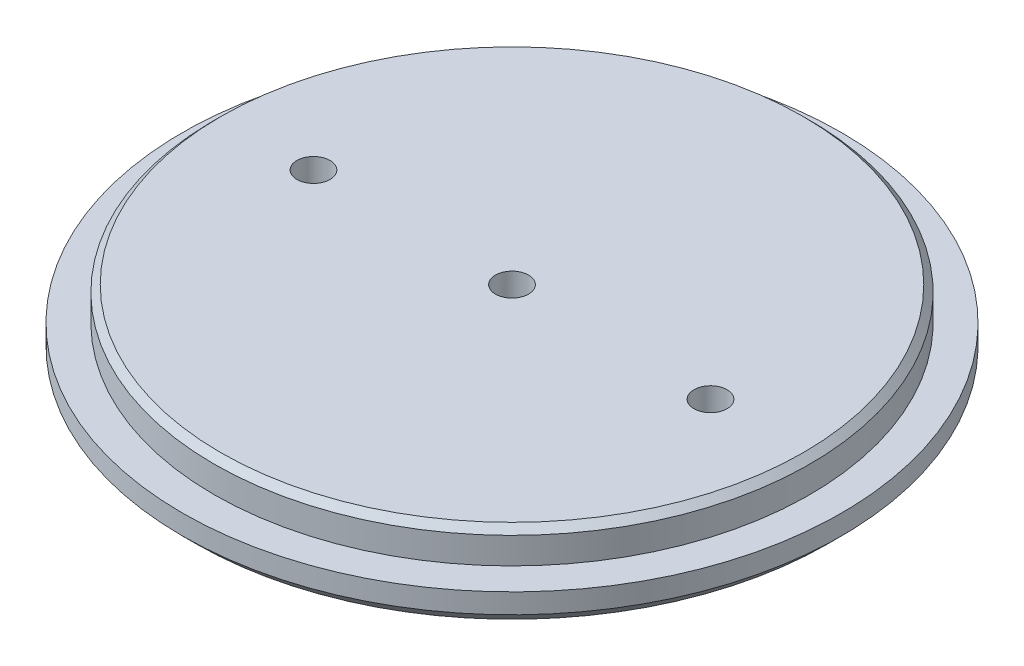
SolidWorks part; units mm, degrees
ref_plane "Front Plane" through (0, 0, 0) normal (0, 0, 1) x (1, 0, 0)
ref_plane "Top Plane" through (0, 0, 0) normal (0, 1, 0) x (1, 0, 0)
ref_plane "Right Plane" through (0, 0, 0) normal (1, 0, 0) x (0, 0, -1)
sketch "Sketch1" plane through (0, 0, 0) normal (0, 1, 0) x (1, 0, 0)
  circle A0 centre (0, 0) radius 63.246
  circle A1 centre (0, 0) radius 63.246 construction
extrude "Boss-Extrude1" add sketch "Sketch1" along normal blind 6.35 contours A0
sketch "Sketch2" plane through (0, 6.35, 0) normal (0, 1, 0) x (1, 0, 0)
  circle A0 centre (0, 0) radius 57.15 construction
  circle A1 centre (0, 0) radius 57.15
extrude "Boss-Extrude2" add sketch "Sketch2" along normal blind 6.35
chamfer "Chamfer1" distance 1.27 angle 45 1 edges at (0, 12.7, 57.15)
sketch "Sketch4" plane through (0, 0, 0) normal (0, -1, 0) x (1, 0, 0)
  line L0 (-38.1, 0) -> (38.1, 0) construction
  circle A0 centre (-38.1, 0) radius 3.175
  circle A1 centre (0, 0) radius 3.175
  circle A2 centre (38.1, 0) radius 3.175
  point P4 (0, 0)
  dimension "D2" = 6.35
  dimension "D1" = 76.2
extrude "Cut-Extrude1" cut sketch "Sketch4" against normal through all
chamfer "Chamfer2" distance 2.54 angle 45 1 edges at (0, 0, 63.246)
